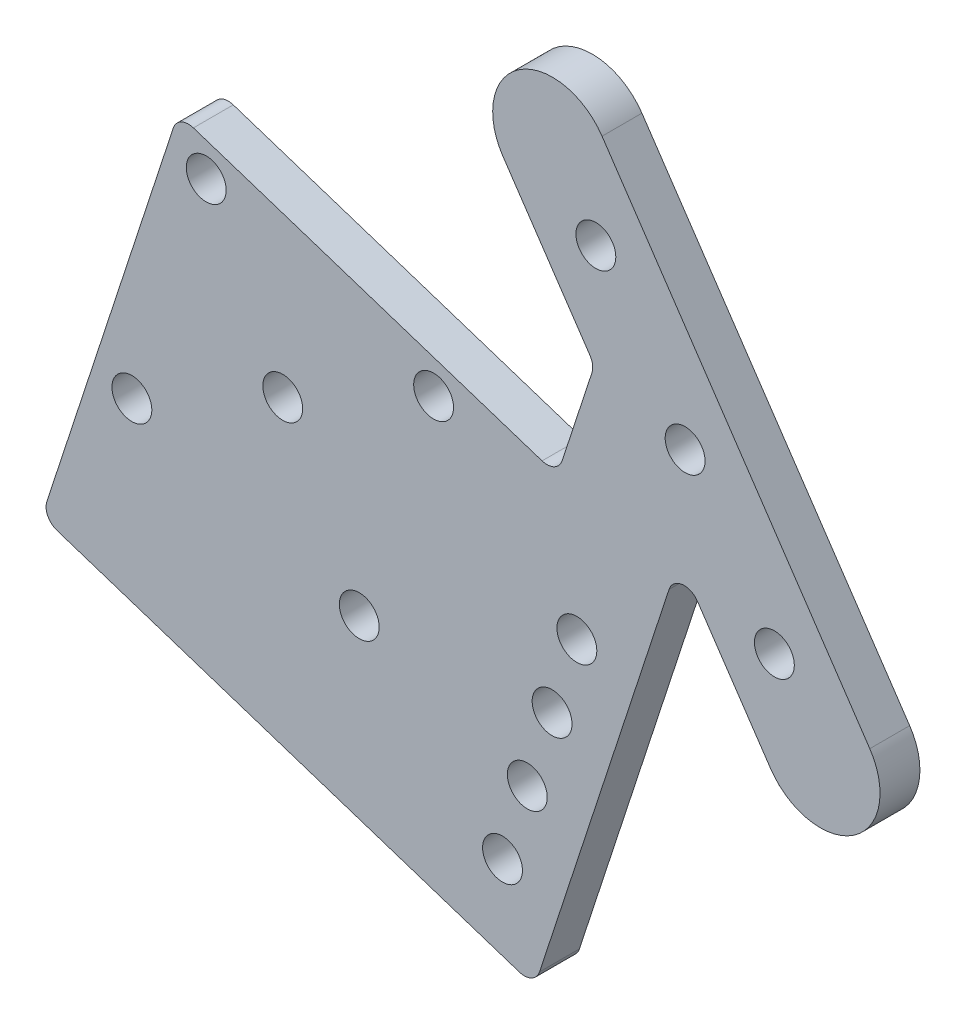
SolidWorks part; units mm, degrees
ref_plane "Front" through (0, 0, 0) normal (0, 0, 1) x (1, 0, 0)
ref_plane "Top" through (0, 0, 0) normal (0, 1, 0) x (1, 0, 0)
ref_plane "Right" through (0, 0, 0) normal (1, 0, 0) x (0, 0, -1)
sketch "Sketch1" plane through (0, 0, 0) normal (0, 0, 1) x (1, 0, 0)
  line L0 (-21.1234, 31.2849) -> (21.5169, -31.8676) construction
  line L1 (-13.2294, 36.615) -> (29.4109, -26.5376)
  line L2 (-29.0175, 25.9549) -> (-14.4487, 4.3778)
  line L6 (-0.946, -15.6205) -> (13.6228, -37.1976)
  line L11 (-14.4487, 4.3778) -> (-42.0816, -80.1186)
  line L12 (-0.946, -15.6205) -> (-23.9752, -86.0399)
  line L13 (-23.9752, -86.0399) -> (-42.0816, -80.1186)
  arc A0 (-13.2294, 36.615) -> (-29.0175, 25.9549) centre (-21.1234, 31.2849) ccw
  arc A1 (13.6228, -37.1976) -> (29.4109, -26.5376) centre (21.5169, -31.8676) ccw
  circle A2 centre (-14.2134, 21.0508) radius 3.175
  circle A3 centre (14.2134, -21.0508) radius 3.175
  circle A4 centre (0, 0) radius 3.175
  circle A5 centre (-29.0809, -71.0083) radius 3.175
  circle A6 centre (-25.1333, -58.9374) radius 3.175
  circle A7 centre (-21.1858, -46.8665) radius 3.175
  circle A8 centre (-17.2382, -34.7956) radius 3.175
  point P3 (0, 0)
  point P17 (0, 0)
  point P20 (0, 0)
  point P21 (0, 0)
  point P22 (0, 0)
  point P27 (0, 0)
  point P31 (0, 0)
  point P32 (0, 0)
  dimension "D2" = 6.35
  dimension "D3" = 25.4
  dimension "D4" = 25.4
  dimension "D5" = 9.525
  dimension "D6" = 63.1525
  dimension "D7" = 19.05
  dimension "D12" = 13.0515
  dimension "D14" = 6.35
  dimension "D15" = 12.7
  dimension "D20" = 12.7
  dimension "D21" = 9.525
  dimension "D22" = 12.7
  dimension "D8" = 26.035
  dimension "D9" = 26.035
  dimension "D10" = 88.9
  dimension "D11" = 76.2
  dimension "D13" = 12.3485
  dimension "D16" = 9.525
  dimension "D17" = 9.525
  dimension "D18" = 12.7
  dimension "D19" = 9.525
extrude "Boss-Extrude2" add sketch "Sketch1" along normal blind 6.35
sketch "Sketch2" plane through (0, 0, 0) normal (0, 0, -1) x (-1, 0, 0)
  line L0 (20.3701, -13.7286) -> (42.0816, -80.1186)
  line L1 (14.4487, 4.3778) -> (42.0816, -80.1186) construction
  line L2 (42.0816, -80.1186) -> (102.4362, -60.3808)
  line L3 (102.4362, -60.3808) -> (80.7246, 6.0092)
  line L4 (80.7246, 6.0092) -> (20.3701, -13.7286)
  dimension "D1" = 69.85
  dimension "D2" = 63.5
extrude "Boss-Extrude3" add sketch "Sketch2" against normal blind 6.35
sketch "Sketch3" plane through (0, 0, 0) normal (0, 0, -1) x (-1, 0, 0)
  line L0 (80.7246, 6.0092) -> (20.3701, -13.7286) construction
  line L1 (43.0732, -11.6487) -> (73.2505, -1.7798)
  line L2 (41.0423, -15.6533) -> (50.9112, -45.8306)
  line L3 (54.9158, -47.8615) -> (85.0931, -37.9926)
  line L4 (77.2551, -3.8107) -> (87.124, -33.988)
  line L5 (40.0555, -12.6356) -> (88.1108, -37.0057) construction
  line L6 (51.8981, -48.8483) -> (76.2682, -0.793) construction
  line L7 (102.4362, -60.3808) -> (80.7246, 6.0092) construction
  circle A0 centre (40.0555, -12.6356) radius 3.175
  circle A1 centre (76.2682, -0.793) radius 3.175
  circle A2 centre (51.8981, -48.8483) radius 3.175
  circle A3 centre (88.1108, -37.0057) radius 3.175
  circle A4 centre (64.0831, -24.8207) radius 3.175
  point P0 (64.0831, -24.8207)
  dimension "D3" = 6.35
  dimension "D4" = 25.4
  dimension "D5" = 24.13
  dimension "D6" = 31.75
  dimension "D1" = 38.1
  dimension "D2" = 38.1
extrude "Cut-Extrude1" cut sketch "Sketch3" against normal blind 6.35 contours A1 | A0 | A2 | A3 | A4
fillet "Fillet1" radius 2.54 6 edges at (-14.4487, 4.3778, 3.175) (-0.946, -15.6205, 3.175) (-23.9752, -86.0399, 3.175) (-102.4362, -60.3808, 3.175) (-80.7246, 6.0092, 3.175) (-20.3701, -13.7286, 3.175)
